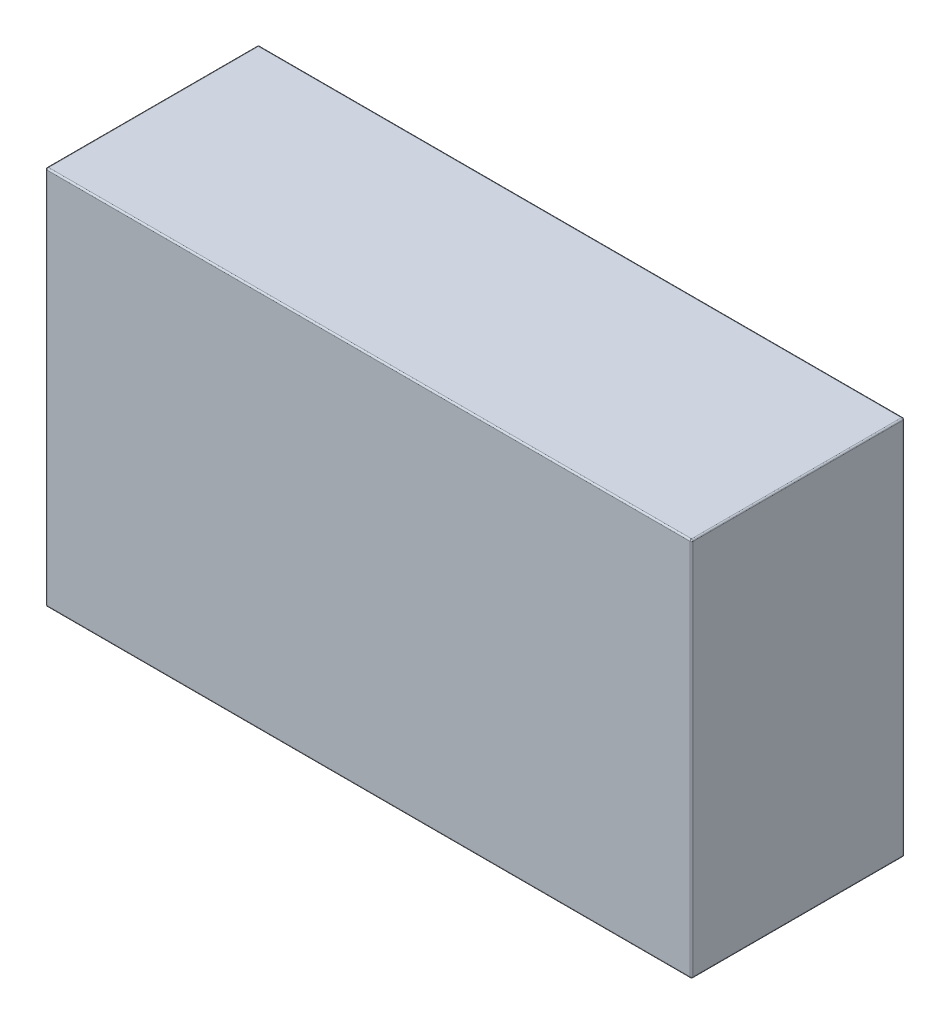
SolidWorks part; units mm, degrees
ref_plane "Front Plane" through (0, 0, 0) normal (0, 0, 1) x (1, 0, 0)
ref_plane "Top Plane" through (0, 0, 0) normal (0, 1, 0) x (1, 0, 0)
ref_plane "Right Plane" through (0, 0, 0) normal (1, 0, 0) x (0, 0, -1)
sketch "Sketch1" plane through (0, 0, 0) normal (0, 0, 1) x (1, 0, 0)
  line L1 (-53.975, 31.75) -> (53.975, 31.75)
  line L2 (-53.975, 31.75) -> (-53.975, -31.75)
  line L3 (-53.975, -31.75) -> (53.975, -31.75)
  line L4 (53.975, 31.75) -> (53.975, -31.75)
  line L5 (-53.975, 31.75) -> (53.975, -31.75) construction
  line L6 (-53.975, -31.75) -> (53.975, 31.75) construction
  point P0 (0, 0)
  dimension "D1" = 107.95
  dimension "D2" = 63.5
extrude "Boss-Extrude1" add sketch "Sketch1" along normal mid plane 35.56
fillet "Fillet1" radius 0.254 12 edges at (0, 31.75, -17.78) (-53.975, 0, -17.78) (0, -31.75, -17.78) (53.975, 0, -17.78) (0, -31.75, 17.78) (-53.975, 0, 17.78) (0, 31.75, 17.78) (53.975, 0, 17.78) (53.975, -31.75, 0) (-53.975, -31.75, 0) (-53.975, 31.75, 0) (53.975, 31.75, 0)
